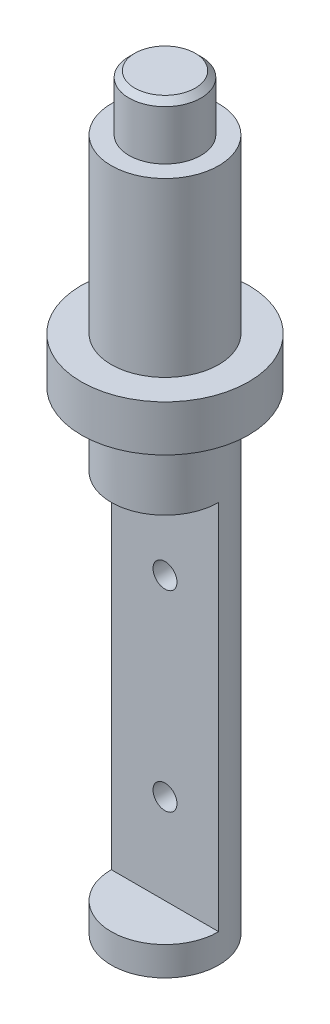
SolidWorks part; units mm, degrees
ref_plane "Front Plane" through (0, 0, 0) normal (0, 0, 1) x (1, 0, 0)
ref_plane "Top Plane" through (0, 0, 0) normal (0, 1, 0) x (1, 0, 0)
ref_plane "Right Plane" through (0, 0, 0) normal (1, 0, 0) x (0, 0, -1)
sketch "Sketch1" plane through (0, 0, 0) normal (0, 1, 0) x (1, 0, 0)
  circle A0 centre (0, 0) radius 28
  dimension "D1" = 56
extrude "Boss-Extrude1" add sketch "Sketch1" against normal blind 118.7 contours A0
sketch "Sketch3" plane through (0, -118.7, 0) normal (0, -1, 0) x (1, 0, 0)
  circle A0 centre (0, 0) radius 43.6
  dimension "D1" = 87.2
extrude "Boss-Extrude2" add sketch "Sketch3" along normal blind 24
sketch "Sketch4" plane through (0, 0, 0) normal (0, 1, 0) x (1, 0, 0)
  circle A0 centre (0, 0) radius 18.75
  circle A1 centre (0, 0) radius 28
  dimension "D1" = 37.5
  dimension "D2" = 56
extrude "Cut-Extrude1" cut sketch "Sketch4" against normal blind 28.9
chamfer "Chamfer1" distance 3 angle 45 1 edges at (0, 0, 18.75)
sketch "Sketch6" plane through (0, -142.7, 0) normal (0, -1, 0) x (1, 0, 0)
  circle A0 centre (0, 0) radius 28
  dimension "D1" = 56
extrude "Boss-Extrude3" add sketch "Sketch6" along normal blind 38.2
sketch "Sketch8" plane through (0, -180.9, 0) normal (0, -1, 0) x (1, 0, 0)
  line L0 (-28, 0) -> (28, 0)
  arc A1 (-28, 0) -> (28, 0) centre (0, 0) ccw
  dimension "D1" = 56
extrude "Boss-Extrude4" add sketch "Sketch8" along normal blind 193.8
sketch "Sketch9" plane through (0, -374.7, 0) normal (0, -1, 0) x (1, 0, 0)
  circle A0 centre (0, 0) radius 28
  dimension "D1" = 56
extrude "Boss-Extrude5" add sketch "Sketch9" along normal blind 15.1
sketch "Sketch10" plane through (0, 0, 0) normal (0, 0, 1) x (1, 0, 0)
  circle A0 centre (0, -227.8) radius 6.25
  circle A1 centre (0, -327.8) radius 6.25
  dimension "D1" = 12.5
  dimension "D2" = 2
extrude "Cut-Extrude2" cut sketch "Sketch10" against normal blind 28.1
